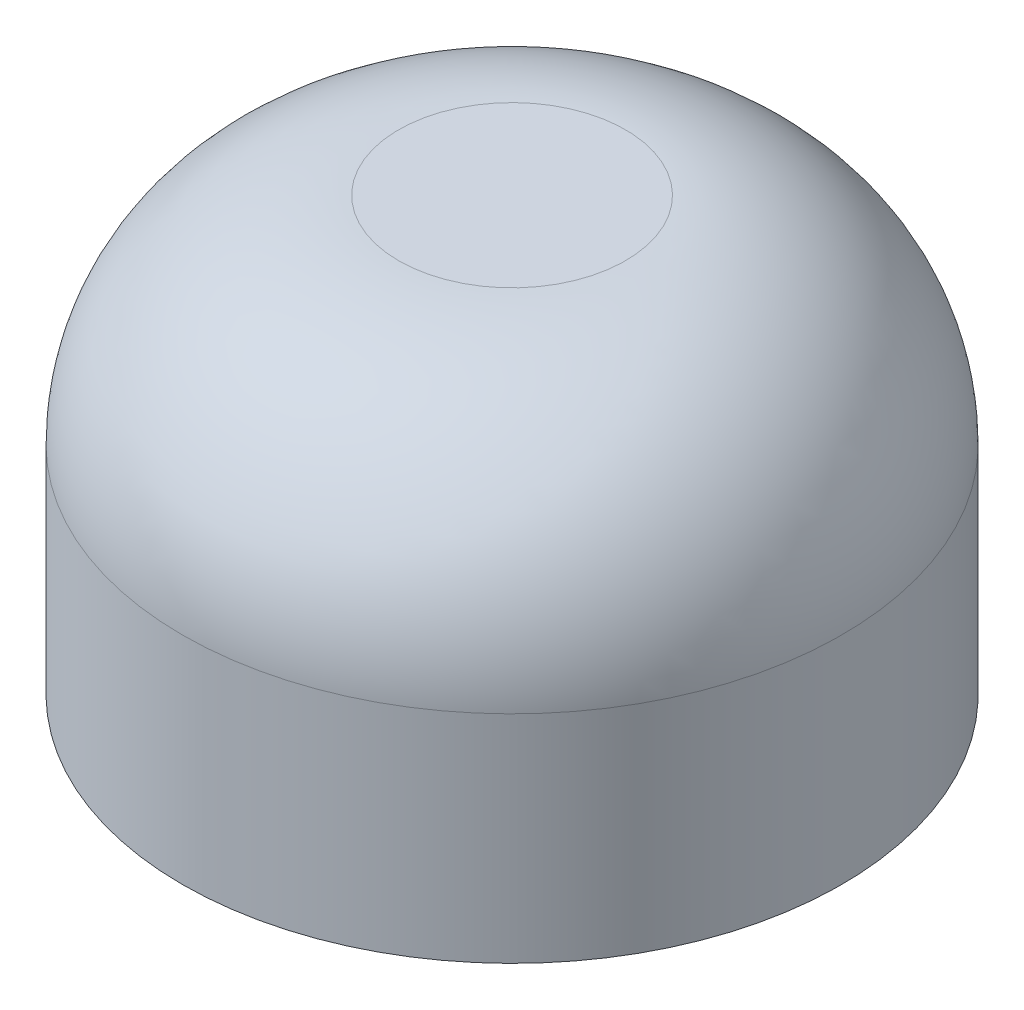
SolidWorks part; units mm, degrees
material "ABS"
ref_plane "Front Plane" through (0, 0, 0) normal (0, 0, 1) x (1, 0, 0)
ref_plane "Top Plane" through (0, 0, 0) normal (0, 1, 0) x (1, 0, 0)
ref_plane "Right Plane" through (0, 0, 0) normal (1, 0, 0) x (0, 0, -1)
sketch "Sketch1" plane through (0, 0, 0) normal (0, 1, 0) x (1, 0, 0)
  circle A0 centre (0, 0) radius 1.55
  circle A1 centre (0, 0) radius 3.05
  dimension "D1" = 3.1
  dimension "D2" = 1.5
extrude "Boss-Extrude1" add sketch "Sketch1" along normal blind 2
sketch "Sketch3" plane through (0, 2, 0) normal (0, 1, 0) x (1, 0, 0)
  circle A0 centre (0, 0) radius 3.05
extrude "Boss-Extrude2" add sketch "Sketch3" along normal blind 2
fillet "Fillet1" radius 2 1 edges at (0, 4, 3.05)
